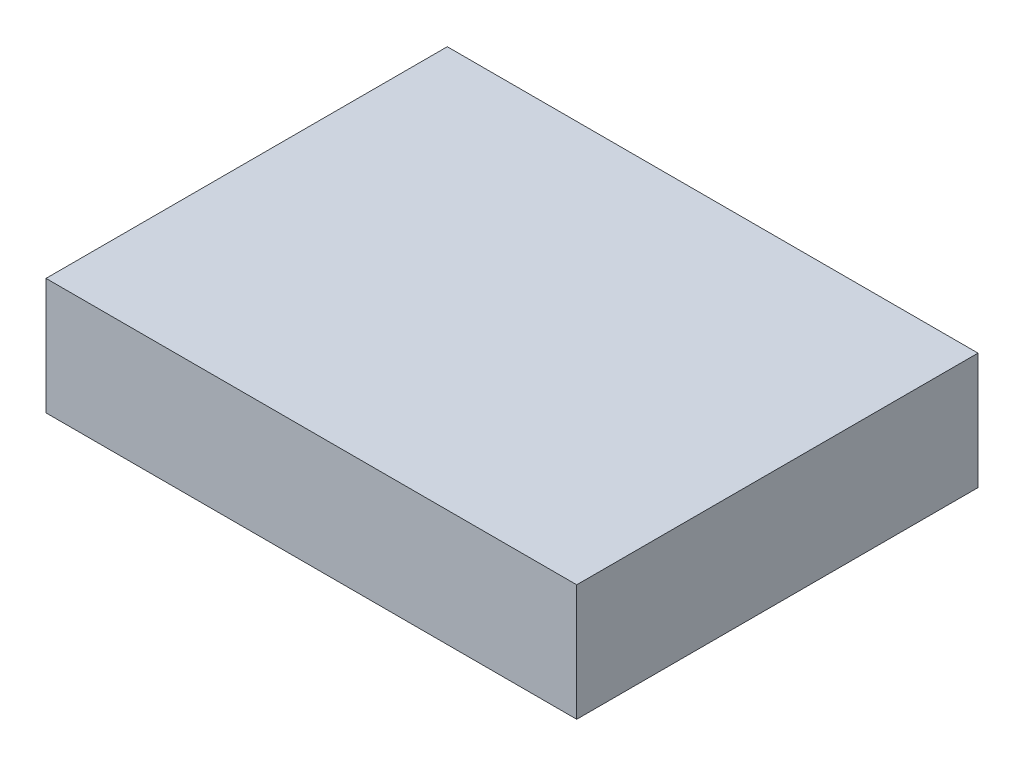
SolidWorks part; units mm, degrees
ref_plane "Front Plane" through (0, 0, 0) normal (0, 0, 1) x (1, 0, 0)
ref_plane "Top Plane" through (0, 0, 0) normal (0, 1, 0) x (1, 0, 0)
ref_plane "Right Plane" through (0, 0, 0) normal (1, 0, 0) x (0, 0, -1)
sketch "Sketch1" plane through (0, 0, 0) normal (0, 1, 0) x (1, 0, 0)
  line L1 (0, 0) -> (41, 0)
  line L2 (0, 0) -> (0, 31)
  line L3 (0, 31) -> (41, 31)
  line L4 (41, 0) -> (41, 31)
  dimension "D1" = 41
  dimension "D2" = 31
extrude "Boss-Extrude1" add sketch "Sketch1" along normal blind 9
